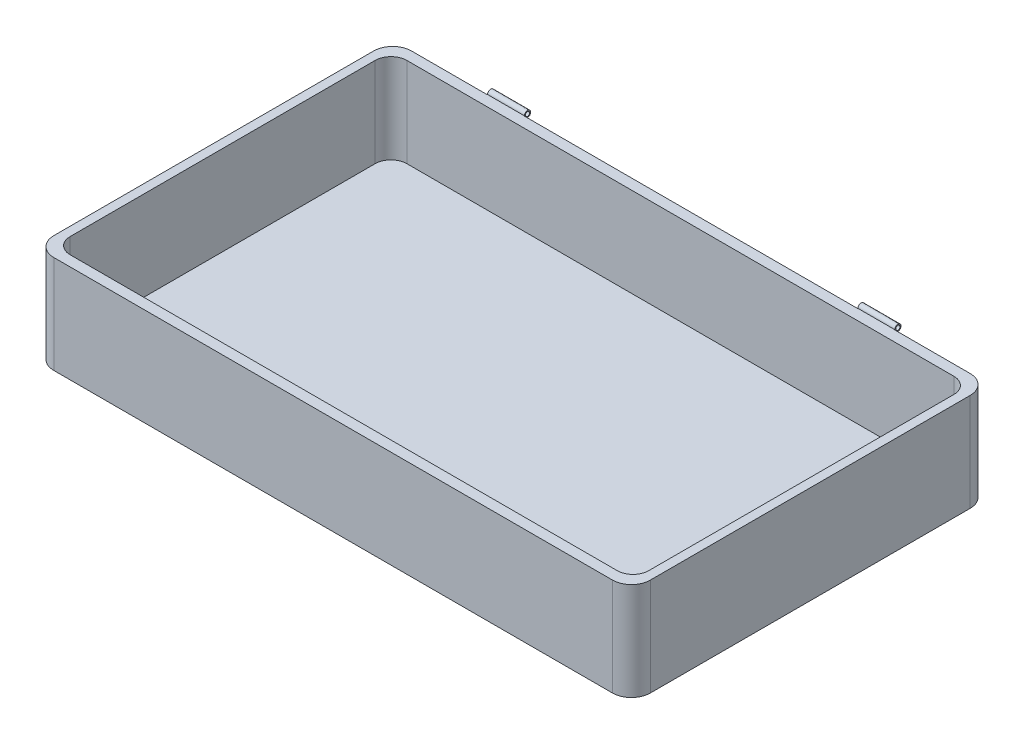
SolidWorks part; units mm, degrees
ref_plane "Front Plane" through (0, 0, 0) normal (0, 0, 1) x (1, 0, 0)
ref_plane "Top Plane" through (0, 0, 0) normal (0, 1, 0) x (1, 0, 0)
ref_plane "Right Plane" through (0, 0, 0) normal (1, 0, 0) x (0, 0, -1)
sketch "Sketch2" plane through (0, 0, 0) normal (0, 1, 0) x (1, 0, 0)
  line L1 (-283.5, -170) -> (283.5, -170)
  line L2 (-283.5, -170) -> (-283.5, 170)
  line L3 (-283.5, 170) -> (283.5, 170)
  line L4 (283.5, -170) -> (283.5, 170)
  line L5 (-283.5, -170) -> (283.5, 170) construction
  line L6 (-283.5, 170) -> (283.5, -170) construction
  point P0 (0, 0)
  dimension "D1" = 567
  dimension "D2" = 340
extrude "Boss-Extrude1" add sketch "Sketch2" along normal blind 93
sketch "Sketch1" plane through (0, 93, 0) normal (0, 1, 0) x (1, 0, 0)
  line L1 (-260, -160) -> (260, -160)
  line L2 (-275, -145) -> (-275, 145)
  line L3 (-260, 160) -> (260, 160)
  line L4 (275, -145) -> (275, 145)
  line L5 (-275, -160) -> (275, 160) construction
  line L6 (-275, 160) -> (275, -160) construction
  arc A0 (260, -160) -> (275, -145) centre (260, -145) ccw
  arc A1 (-275, -145) -> (-260, -160) centre (-260, -145) ccw
  arc A2 (275, 145) -> (260, 160) centre (260, 145) ccw
  arc A3 (-275, 145) -> (-260, 160) centre (-260, 145) cw
  point P0 (0, 0)
  dimension "D3" = 15
  dimension "D1" = 550
  dimension "D2" = 320
extrude "Cut-Extrude1" cut sketch "Sketch1" against normal blind 85
fillet "Fillet1" radius 18 4 edges at (-283.5, 46.5, -170) (-283.5, 46.5, 170) (283.5, 46.5, -170) (283.5, 46.5, 170)
ref_plane "Plane1" through (193.5, 0, 0) normal (1, 0, 0) x (0, 0, -1)
sketch "Sketch3" plane through (193.5, 0, 0) normal (1, 0, 0) x (0, 0, -1)
  line L0 (152, 93) -> (182, 93) construction
  circle A0 centre (173.25, 93) radius 3
  point P4 (0, 0)
  point P6 (0, 0)
  point P7 (0, 0)
  point P8 (0, 0)
  point P9 (171.1955, 93)
  point P10 (170, 93)
  point P11 (171.2574, 93)
  point P12 (0, 0)
  dimension "D1" = 6
  dimension "D2" = 30
  dimension "D3" = 18
  dimension "D4" = 3.25
extrude "Boss-Extrude2" add sketch "Sketch3" against normal blind 35
sketch "Sketch4" plane through (193.5, 0, 0) normal (1, 0, 0) x (0, 0, -1)
  circle A0 centre (173.25, 93) radius 2
  circle A1 centre (173.25, 93) radius 3 construction
  dimension "D1" = 4
extrude "Cut-Extrude2" cut sketch "Sketch4" against normal through all
sketch "Sketch5" plane through (193.5, 0, 0) normal (1, 0, 0) x (0, 0, -1)
  line L0 (170, 93) -> (152, 93) construction
  line L1 (170, 93) -> (171, 93)
  line L2 (170, 93) -> (170, 92)
  line L3 (170, 92) -> (171, 92)
  line L4 (171, 93) -> (171, 92)
  point P6 (0, 0)
  dimension "D1" = 1
  dimension "D2" = 1
extrude "Boss-Extrude3" add sketch "Sketch5" against normal blind 35
mirror "Mirror5" about plane through (0, 0, 0) normal (1, 0, 0) of "Boss-Extrude3", "Cut-Extrude2", "Boss-Extrude2"
mirror "Mirror6" about plane through (0, 0, 0) normal (1, 0, 0) of "Boss-Extrude2"
mirror "Mirror7" about plane through (0, 0, 0) normal (1, 0, 0) of "Cut-Extrude2"
